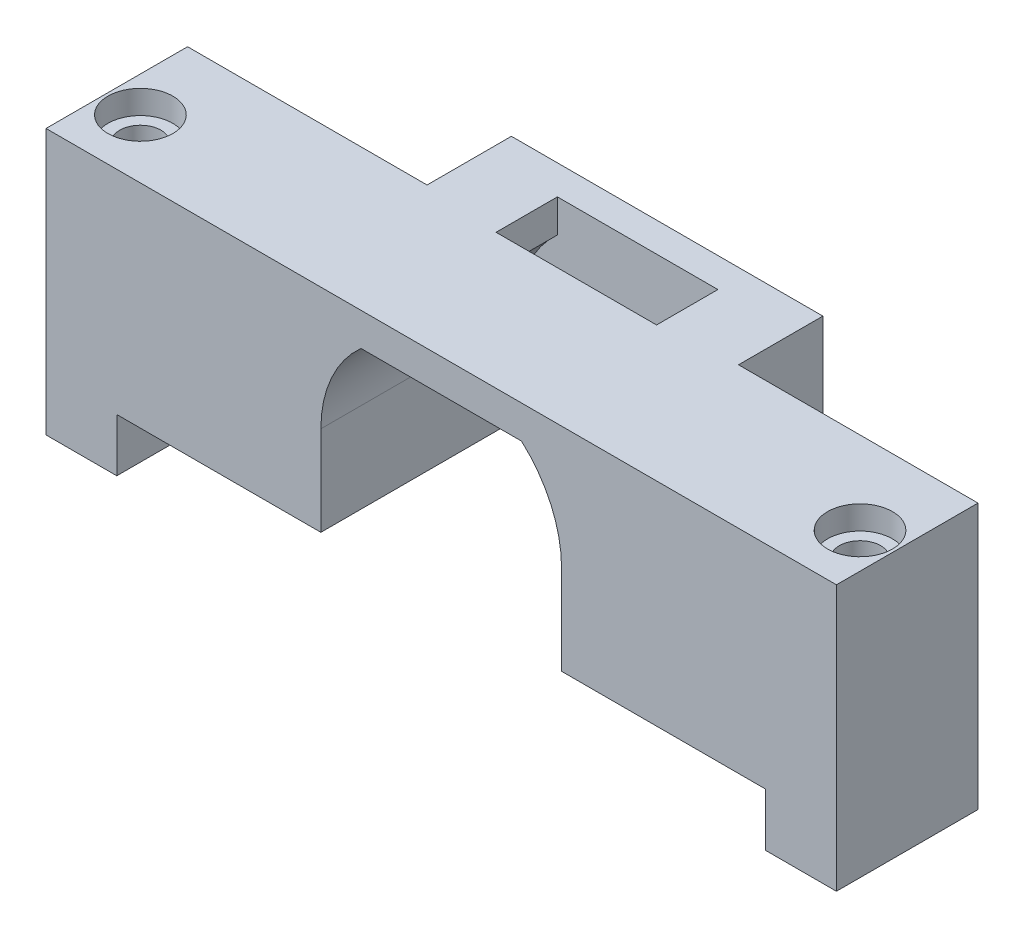
SolidWorks part; units mm, degrees
ref_plane "Front Plane" through (0, 0, 0) normal (0, 0, 1) x (1, 0, 0)
ref_plane "Top Plane" through (0, 0, 0) normal (0, 1, 0) x (1, 0, 0)
ref_plane "Right Plane" through (0, 0, 0) normal (1, 0, 0) x (0, 0, -1)
sketch "Sketch1" plane through (0, 0, 0) normal (0, 0, 1) x (1, 0, 0)
  line L0 (27.5, 0) -> (27.5, 18) construction
  line L1 (0, 0) -> (17.3, 0)
  line L2 (0, 0) -> (0, 18)
  line L3 (0, 18) -> (55, 18)
  line L4 (55, 0) -> (55, 18)
  line L5 (20.6971, 15.2) -> (34.3029, 15.2)
  line L7 (17.3, 0) -> (17.3, 7.6)
  line L8 (37.7, 0) -> (37.7, 7.6)
  line L9 (20.6971, 15.2) -> (34.3029, 15.2)
  line L10 (17.3, 0) -> (37.7, 15.2) construction
  line L11 (17.3, 15.2) -> (37.7, 0) construction
  line L12 (0, 15.2) -> (55, 15.2) construction
  line L13 (37.7, 0) -> (55, 0)
  line L14 (0, 0) -> (55, 0) construction
  line L15 (17.3, 7.6) -> (17.3, 15.2)
  line L16 (17.3, 15.2) -> (37.7, 15.2)
  line L17 (37.7, 15.2) -> (37.7, 7.6)
  arc A2 (20.6971, 15.2) -> (17.3, 7.6) centre (27.5, 7.6) ccw
  arc A3 (37.7, 7.6) -> (34.3029, 15.2) centre (27.5, 7.6) ccw
  dimension "D3" = 10.2
  dimension "D6" = 20.4
  dimension "D1" = 55
  dimension "D2" = 18
  dimension "D5" = 10.2
  dimension "D4" = 15.2
extrude "Boss-Extrude2" add sketch "Sketch1" along normal blind 12 contours L16 L17 L8 L13 L4 L3 L2 L1 L7 L15 L5 | A2 L16 L15 | A3 L17 L16
sketch "Sketch2" plane through (0, 0, 0) normal (-1, 0, 0) x (0, 0, 1)
  line L0 (12, 0) -> (12, 18) construction
  line L5 (12, 0) -> (0, 0) construction
  line L6 (0, 18) -> (12, 18)
  line L7 (0, 18) -> (0, -4.5)
  line L8 (0, -4.5) -> (12, -4.5)
  line L9 (12, 18) -> (12, -4.5)
  dimension "D1" = 4.5
extrude "Boss-Extrude3" add sketch "Sketch2" along normal blind 6
sketch "Sketch3" plane through (55, 0, 0) normal (1, 0, 0) x (0, 0, -1)
  line L1 (-12, 18) -> (0, 18)
  line L2 (-12, 18) -> (-12, -4.5)
  line L3 (-12, -4.5) -> (0, -4.5)
  line L4 (0, 18) -> (0, -4.5)
extrude "Boss-Extrude4" add sketch "Sketch3" along normal blind 6
sketch "Sketch4" plane through (0, 18, 0) normal (0, 1, 0) x (1, 0, 0)
  line L0 (0, 0) -> (0, -12) construction
  line L1 (-6, -12) -> (-6, 0) construction
  line L3 (27.5, 0) -> (27.5, -12) construction
  line L4 (-6, 0) -> (61, 0) construction
  line L5 (-6, -12) -> (61, -12) construction
  line L6 (0, 0) -> (0, -12) construction
  circle A0 centre (-3, -7) radius 1.75
  circle A1 centre (58, -7) radius 1.75
  dimension "D1" = 3.5
  dimension "D2" = 3
  dimension "D3" = 5
extrude "Cut-Extrude1" cut sketch "Sketch4" against normal up to surface (22.5 mm away) up to face at (-3, -4.5, 6)
sketch "Sketch5" plane through (0, 0, 0) normal (0, 0, -1) x (-1, 0, 0)
  line L0 (-37.7, 7.6) -> (-17.3, 7.6) construction
  line L1 (-37.7, 0) -> (-40.7, 0)
  line L2 (-37.7, 0) -> (-55, 0) construction
  line L3 (-40.7, 0) -> (-40.7, 18)
  line L4 (6, 18) -> (-61, 18) construction
  line L5 (-40.7, 18) -> (-14.3, 18)
  line L6 (-27.5, 18) -> (-27.5, 0) construction
  line L7 (-17.3, 6) -> (-17.3, 0)
  line L8 (-20.6971, 15.2) -> (-34.3029, 15.2) construction
  line L9 (-37.7, 7.6) -> (-37.7, 0) construction
  line L10 (-20.6971, 15.2) -> (-34.3029, 15.2)
  line L11 (-37.7, 6) -> (-37.7, 0)
  line L12 (-14.3, 0) -> (-14.3, 18)
  line L13 (-17.3, 0) -> (-14.3, 0)
  arc A0 (-37.7, 6) -> (-37.5745, 6.0049) centre (-37.7, 7.6) ccw
  arc A1 (-34.3029, 15.2) -> (-37.7, 7.6) centre (-27.5, 7.6) ccw construction
  arc A2 (-34.3029, 15.2) -> (-37.5745, 9.1951) centre (-27.5, 7.6) ccw
  arc A3 (-20.6971, 15.2) -> (-17.4255, 9.1951) centre (-27.5, 7.6) cw
  arc A4 (-17.3, 6) -> (-17.4255, 6.0049) centre (-17.3, 7.6) cw
  arc A5 (-17.4255, 6.0049) -> (-20.6971, 15.2) centre (-27.5, 7.6) ccw
  arc A6 (-34.3029, 15.2) -> (-37.5745, 6.0049) centre (-27.5, 7.6) ccw
  point P22 (-27.5, 15.2)
  dimension "D1" = 3.2
  dimension "D2" = 3
extrude "Boss-Extrude5" add sketch "Sketch5" along normal blind 4.65
sketch "Sketch6" plane through (0, 0, -4.65) normal (0, 0, -1) x (-1, 0, 0)
  line L0 (-27.5, 18) -> (-27.5, 0) construction
  line L1 (-14.3, 18) -> (-40.7, 18) construction
  line L2 (-36.1012, 7.5372) -> (-18.8988, 7.5372) construction
  line L3 (-40.7, 18) -> (-40.7, 0)
  line L4 (-40.7, 0) -> (-37.7, 0) construction
  line L5 (-40.7, 18) -> (-40.7, 0) construction
  line L6 (-40.7, 0) -> (-14.3, 0)
  line L7 (-17.3, 0) -> (-14.3, 0) construction
  line L8 (-14.3, 0) -> (-14.3, 18)
  line L9 (-14.3, 18) -> (-40.7, 18)
  arc A0 (-37.7, 6) -> (-37.5745, 9.1951) centre (-37.7, 7.6) ccw construction
  arc A1 (-17.4255, 9.1951) -> (-17.3, 6) centre (-17.3, 7.6) ccw construction
  circle A2 centre (-27.5, 7.5372) radius 4.925
  dimension "D1" = 9.85
extrude "Boss-Extrude6" add sketch "Sketch6" along normal blind 2.5
sketch "Sketch7" plane through (0, 18, 0) normal (0, 1, 0) x (1, 0, 0)
  circle A0 centre (-3, -7) radius 2.75
  circle A1 centre (58, -7) radius 2.75
  dimension "D1" = 5.5
  dimension "D2" = 5.5
extrude "Cut-Extrude2" cut sketch "Sketch7" against normal blind 2
sketch "Sketch12" plane through (0, 0, -7.15) normal (0, 0, -1) x (-1, 0, 0)
  line L0 (-40.7, 0) -> (-14.3, 0) construction
  line L1 (-22.5946, 7.0978) -> (-32.425, 7.0978)
  line L2 (-22.5946, 7.0978) -> (-22.5946, 0)
  line L3 (-22.5946, 0) -> (-32.425, 0)
  line L4 (-32.425, 7.0978) -> (-32.425, 0)
  circle A0 centre (-27.5, 7.5372) radius 4.925 construction
extrude "Cut-Extrude12" cut sketch "Sketch12" against normal up to surface (2.5 mm away)
sketch "Sketch13" plane through (0, 0, 0) normal (0, 0, 1) x (1, 0, 0)
  line L0 (17.3, 7.6) -> (17.3, 6) construction
  line L1 (37.7, 6) -> (37.7, 7.6) construction
  line L2 (17.3, 7.6) -> (17.3, 6)
  line L3 (37.7, 6) -> (37.7, 7.6)
  arc A0 (17.3, 6) -> (17.4255, 9.1951) centre (17.3, 7.6) ccw construction
  arc A1 (17.4255, 9.1951) -> (17.3, 7.6) centre (27.5, 7.6) ccw construction
  arc A2 (37.7, 7.6) -> (37.5745, 9.1951) centre (27.5, 7.6) ccw construction
  arc A3 (37.5745, 9.1951) -> (37.7, 6) centre (37.7, 7.6) ccw construction
  arc A4 (17.3, 6) -> (17.4255, 9.1951) centre (17.3, 7.6) ccw
  arc A5 (17.4255, 9.1951) -> (17.3, 7.6) centre (27.5, 7.6) ccw
  arc A6 (37.7, 7.6) -> (37.5745, 9.1951) centre (27.5, 7.6) ccw
  arc A7 (37.5745, 9.1951) -> (37.7, 6) centre (37.7, 7.6) ccw
extrude "Cut-Extrude13" cut sketch "Sketch13" against normal up to surface (4.65 mm away)
sketch "Sketch14" plane through (0, 15.2, 0) normal (0, -1, 0) x (-1, 0, 0)
  line L0 (-34.3029, -12) -> (-34.3029, 4.65) construction
  line L1 (-34.3029, -0.55) -> (-20.6971, -0.55)
  line L2 (-34.3029, -0.55) -> (-34.3029, 4.65)
  line L3 (-34.3029, 4.65) -> (-20.6971, 4.65)
  line L4 (-20.6971, -0.55) -> (-20.6971, 4.65)
  dimension "D1" = 5.2
extrude "Cut-Extrude14" cut sketch "Sketch14" against normal up to surface (2.8 mm away) contours L2 L1 L4 L3
